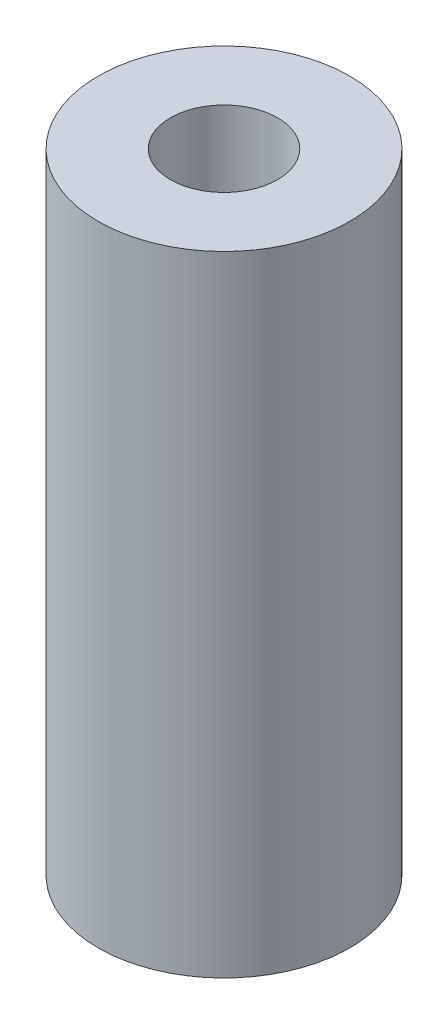
SolidWorks part; units mm, degrees
ref_plane "Front Plane" through (0, 0, 0) normal (0, 0, 1) x (1, 0, 0)
ref_plane "Top Plane" through (0, 0, 0) normal (0, 1, 0) x (1, 0, 0)
ref_plane "Right Plane" through (0, 0, 0) normal (1, 0, 0) x (0, 0, -1)
sketch "Sketch1" plane through (0, 0, 0) normal (0, 1, 0) x (1, 0, 0)
  circle A0 centre (0, 0) radius 3.175
  circle A1 centre (0, 0) radius 1.3525
  dimension "D1" = 2.7051
  dimension "D2" = 6.35
extrude "Extrude1" add sketch "Sketch1" along normal blind 15.875
